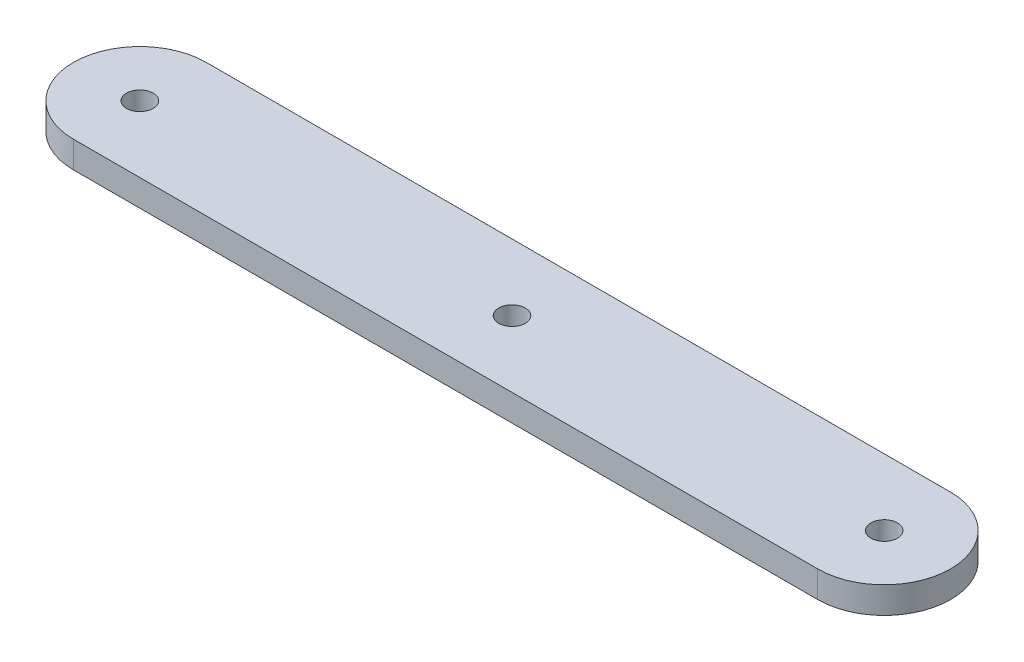
SolidWorks part; units mm, degrees
ref_plane "Piano frontale" through (0, 0, 0) normal (0, 0, 1) x (1, 0, 0)
ref_plane "Piano superiore" through (0, 0, 0) normal (0, 1, 0) x (1, 0, 0)
ref_plane "Piano destro" through (0, 0, 0) normal (1, 0, 0) x (0, 0, -1)
sketch "Schizzo1" plane through (0, 0, 0) normal (0, 1, 0) x (1, 0, 0)
  line L0 (-14, 0) -> (14, 0) construction
  line L1 (-14, 2.5) -> (14, 2.5)
  line L2 (-14, -2.5) -> (14, -2.5)
  line L3 (-14, 0) -> (-16.5, 0) construction
  line L4 (14, 0) -> (16.5, 0) construction
  arc A0 (-14, 2.5) -> (-14, -2.5) centre (-14, 0) ccw
  arc A1 (14, -2.5) -> (14, 2.5) centre (14, 0) ccw
  circle A2 centre (0, 0) radius 0.5
  circle A3 centre (-14, 0) radius 0.5
  circle A4 centre (14, 0) radius 0.5
  point P2 (0, 0)
  dimension "D1" = 1
  dimension "D2" = 28
  dimension "D4" = 1
  dimension "D5" = 1
  dimension "D3" = 5
extrude "Estrusione-Estrusione3" add sketch "Schizzo1" along normal mid plane 1
